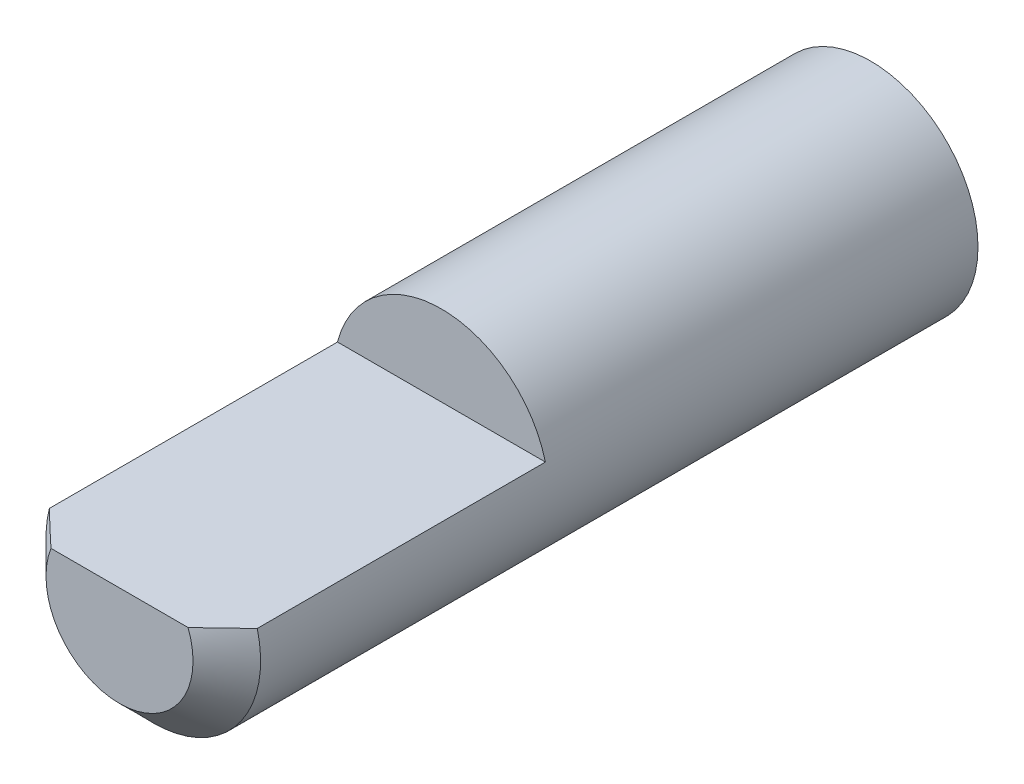
SolidWorks part; units mm, degrees
ref_plane "Front Plane" through (0, 0, 0) normal (0, 0, 1) x (1, 0, 0)
ref_plane "Top Plane" through (0, 0, 0) normal (0, 1, 0) x (1, 0, 0)
ref_plane "Right Plane" through (0, 0, 0) normal (1, 0, 0) x (0, 0, -1)
sketch "Sketch1" plane through (0, 0, 0) normal (0, 0, 1) x (1, 0, 0)
  circle A0 centre (0, 0) radius 3.175
  dimension "D1" = 6.35
extrude "Boss-Extrude1" add sketch "Sketch1" along normal blind 22.225
sketch "Sketch3" plane through (0, 0, 22.225) normal (0, 0, 1) x (1, 0, 0)
  line L0 (-3.0758, 0.7874) -> (3.0758, 0.7874)
  circle A0 centre (0, 0) radius 3.175 construction
  point P4 (0, -3.175)
  dimension "D1" = 3.9624
extrude "Cut-Extrude1" cut sketch "Sketch3" against normal blind 9.525 and the other way through all
chamfer "Chamfer1" distance 1 angle 45 1 edges at (0, -3.175, 22.225)
